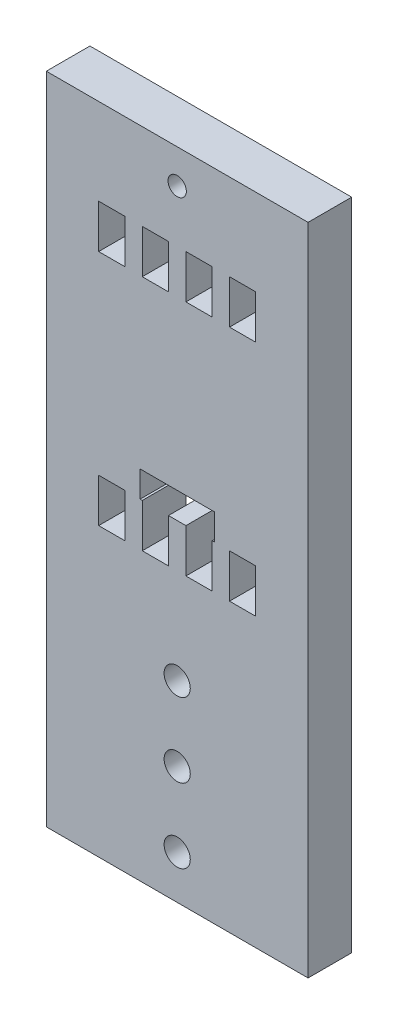
SolidWorks part; units mm, degrees
ref_plane "Plan de face" through (0, 0, 0) normal (0, 0, 1) x (1, 0, 0)
ref_plane "Plan de dessus" through (0, 0, 0) normal (0, 1, 0) x (1, 0, 0)
ref_plane "Plan de droite" through (0, 0, 0) normal (1, 0, 0) x (0, 0, -1)
sketch "Esquisse1" plane through (0, 0, 0) normal (0, 0, 1) x (1, 0, 0)
  line L0 (14, 32.9) -> (14, 37.9)
  line L1 (0, 0) -> (30, 0)
  line L2 (0, 0) -> (0, 70)
  line L3 (0, 70) -> (30, 70)
  line L4 (30, 0) -> (30, 70)
  line L5 (6, 32.9) -> (9, 32.9)
  line L6 (6, 32.9) -> (6, 37.9)
  line L7 (6, 37.9) -> (9, 37.9)
  line L8 (9, 32.9) -> (9, 37.9)
  line L9 (11, 37.9) -> (14, 37.9)
  line L10 (11, 32.9) -> (11, 37.9)
  line L11 (11, 32.9) -> (14, 32.9)
  line L12 (19, 32.9) -> (19, 37.9)
  line L13 (16, 37.9) -> (19, 37.9)
  line L14 (16, 32.9) -> (16, 37.9)
  line L15 (16, 32.9) -> (19, 32.9)
  line L16 (24, 32.9) -> (24, 37.9)
  line L17 (21, 37.9) -> (24, 37.9)
  line L18 (21, 32.9) -> (21, 37.9)
  line L19 (21, 32.9) -> (24, 32.9)
  line L20 (0, 49) -> (30, 49) construction
  line L21 (21, 65.1) -> (24, 65.1)
  line L22 (21, 65.1) -> (21, 60.1)
  line L23 (21, 60.1) -> (24, 60.1)
  line L24 (24, 65.1) -> (24, 60.1)
  line L25 (16, 65.1) -> (19, 65.1)
  line L26 (16, 65.1) -> (16, 60.1)
  line L27 (16, 60.1) -> (19, 60.1)
  line L28 (19, 65.1) -> (19, 60.1)
  line L29 (11, 65.1) -> (14, 65.1)
  line L30 (11, 65.1) -> (11, 60.1)
  line L31 (11, 60.1) -> (14, 60.1)
  line L32 (9, 65.1) -> (9, 60.1)
  line L33 (6, 60.1) -> (9, 60.1)
  line L34 (6, 65.1) -> (6, 60.1)
  line L35 (6, 65.1) -> (9, 65.1)
  line L36 (14, 65.1) -> (14, 60.1)
  circle A0 centre (15, 5) radius 1.5
  circle A1 centre (15, 13.5) radius 1.5
  circle A2 centre (15, 22) radius 1.5
  dimension "D3" = 3
  dimension "D4" = 3
  dimension "D5" = 3
  dimension "D1" = 70
  dimension "D2" = 30
  dimension "D6" = 8.5
  dimension "D7" = 8.5
  dimension "D8" = 5
  dimension "D9" = 15
  dimension "D10" = 5
  dimension "D11" = 3
  dimension "D13" = 6
  dimension "D14" = 11.1
  dimension "D15" = 21
  dimension "D12" = 4
extrude "Boss.-Extru.1" add sketch "Esquisse1" along normal blind 5
sketch "Esquisse2" plane through (0, 0, 5) normal (0, 0, 1) x (1, 0, 0)
  line L0 (11, 37.9) -> (11, 32.9) construction
  line L1 (10.75, 37.9) -> (19.25, 37.9)
  line L2 (10.75, 37.9) -> (10.75, 40.9)
  line L3 (10.75, 40.9) -> (19.25, 40.9)
  line L4 (19.25, 37.9) -> (19.25, 40.9)
  dimension "D1" = 3
  dimension "D2" = 8.5
  dimension "D3" = 0.25
extrude "Enlèv. mat.-Extru.1" cut sketch "Esquisse2" against normal blind 5
sketch "Esquisse3" plane through (0, 70, 0) normal (0, 1, 0) x (1, 0, 0)
  line L0 (30, -5) -> (0, -5) construction
  line L1 (0, -5) -> (30, -5)
  line L2 (0, -5) -> (0, 0)
  line L3 (0, 0) -> (30, 0)
  line L4 (30, -5) -> (30, 0)
extrude "Boss.-Extru.2" add sketch "Esquisse3" along normal blind 5
sketch "Esquisse4" plane through (0, 0, 5) normal (0, 0, 1) x (1, 0, 0)
  line L0 (0, 75) -> (0, 0) construction
  line L2 (14, 65.1) -> (11, 65.1) construction
  circle A0 centre (15, 71.1) radius 1.05
  dimension "D1" = 2.1
  dimension "D2" = 15
  dimension "D3" = 6
extrude "Enlèv. mat.-Extru.2" cut sketch "Esquisse4" against normal blind 10
